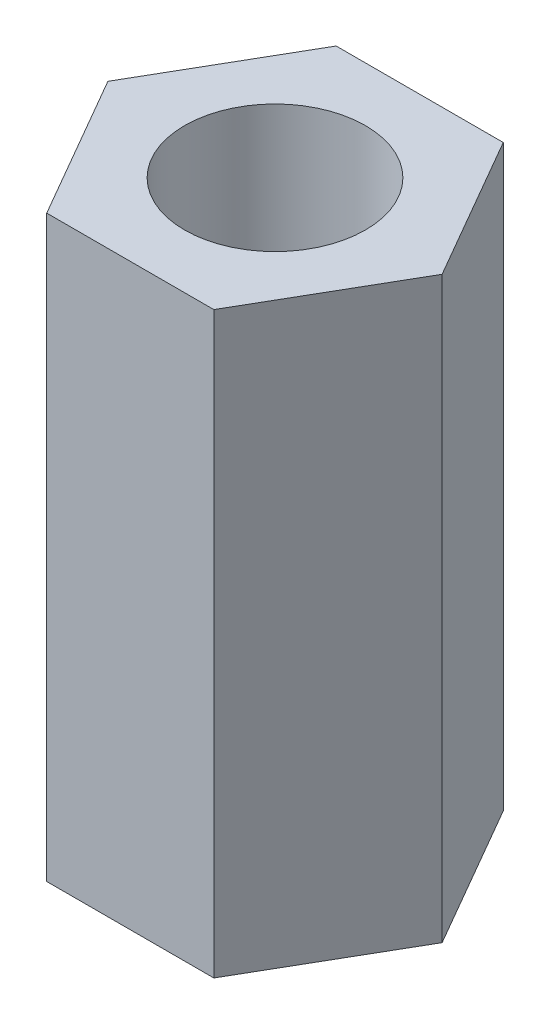
SolidWorks part; units mm, degrees
ref_plane "Front Plane" through (0, 0, 0) normal (0, 0, 1) x (1, 0, 0)
ref_plane "Top Plane" through (0, 0, 0) normal (0, 1, 0) x (1, 0, 0)
ref_plane "Right Plane" through (0, 0, 0) normal (1, 0, 0) x (0, 0, -1)
sketch "Sketch1" plane through (0, 0, 0) normal (0, 1, 0) x (1, 0, 0)
  line L1 (1.8331, -3.175) -> (3.6662, 0)
  line L2 (3.6662, 0) -> (1.8331, 3.175)
  line L3 (1.8331, 3.175) -> (-1.8331, 3.175)
  line L4 (-1.8331, 3.175) -> (-3.6662, 0)
  line L5 (-3.6662, 0) -> (-1.8331, -3.175)
  line L6 (-1.8331, -3.175) -> (1.8331, -3.175)
  circle A0 centre (0, 0) radius 3.175 construction
  circle A1 centre (0, 0) radius 1.9844
  dimension "D2" = 3.9688
  dimension "D1" = 3.175
extrude "Boss-Extrude1" add sketch "Sketch1" along normal blind 12.7
